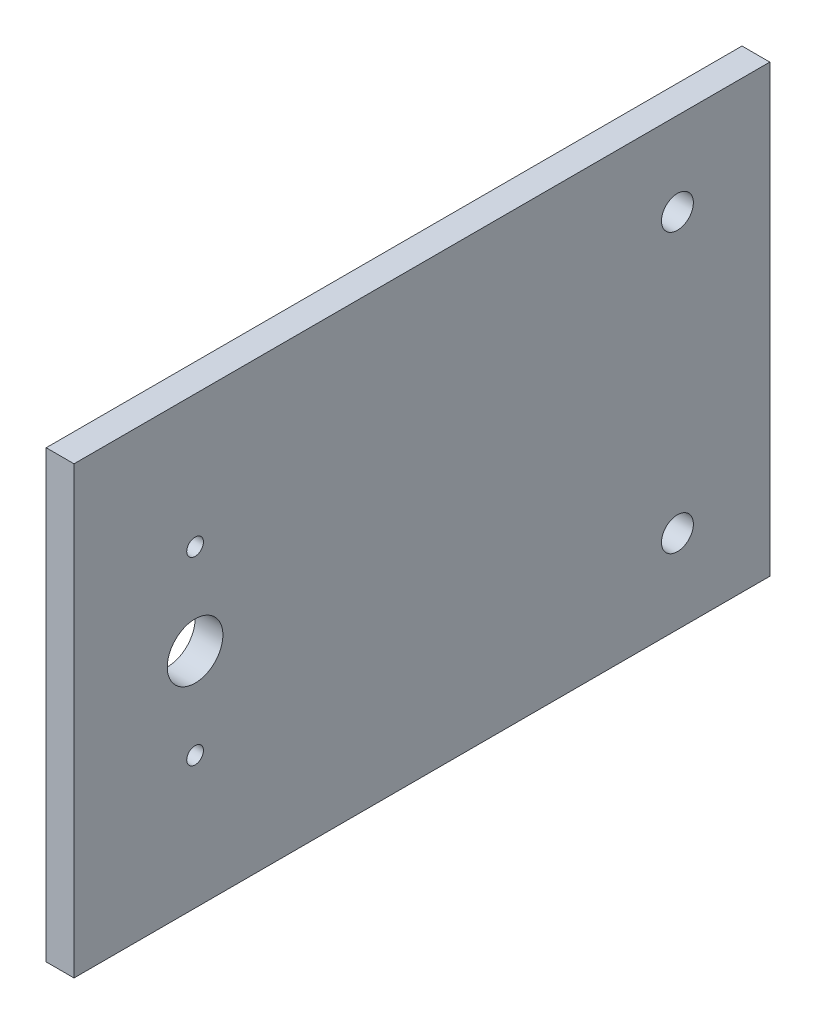
SolidWorks part; units mm, degrees
ref_plane "Front Plane" through (0, 0, 0) normal (1, 0, 0) x (0, 1, 0)
ref_plane "Top Plane" through (0, 0, 0) normal (0, 0, 1) x (0, 1, 0)
ref_plane "Right Plane" through (0, 0, 0) normal (0, 1, 0) x (-1, 0, 0)
sketch "Sketch1" plane through (0, 0, 0) normal (1, 0, 0) x (0, 1, 0)
  line L0 (-40, 40.75) -> (40, 40.75) construction
  line L1 (-40, -62.5) -> (40, -62.5)
  line L2 (-40, -62.5) -> (-40, 62.5)
  line L3 (-40, 62.5) -> (40, 62.5)
  line L4 (40, -62.5) -> (40, 62.5)
  line L5 (-40, -62.5) -> (40, 62.5) construction
  line L6 (-40, 62.5) -> (40, -62.5) construction
  line L7 (0, 62.5) -> (0, -62.5) construction
  line L8 (-40, -45.9) -> (40, -45.9) construction
  circle A5 centre (0, 40.75) radius 5
  circle A6 centre (-16.22, 40.75) radius 1.5
  circle A7 centre (16.22, 40.75) radius 1.5
  circle A8 centre (-25, -45.9) radius 2.8668
  circle A9 centre (25, -45.9) radius 2.8668
  point P0 (0, 0)
  point P20 (-20.1909, -54.2)
  dimension "D5" = 3
  dimension "D4" = 16.22
  dimension "D6" = 16.6
  dimension "D8" = 10
  dimension "D1" = 125
  dimension "D2" = 80
  dimension "D3" = 103.25
  dimension "D7" = 25
extrude "Boss-Extrude1" add sketch "Sketch1" along normal blind 5
